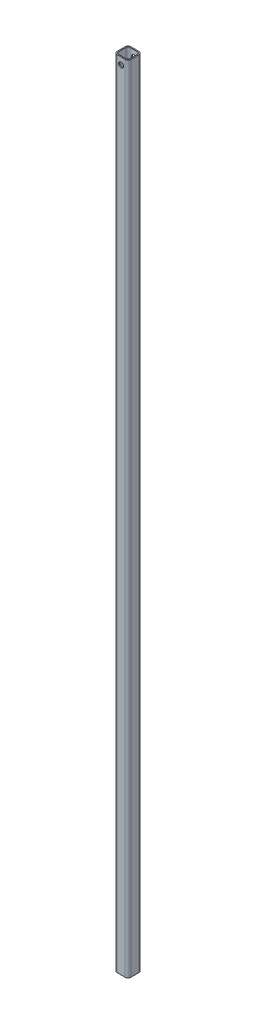
SolidWorks part; units mm, degrees
material "Plain Carbon Steel"
ref_plane "Front Plane" through (0, 0, 0) normal (0, 0, 1) x (1, 0, 0)
ref_plane "Top Plane" through (0, 0, 0) normal (0, 1, 0) x (1, 0, 0)
ref_plane "Right Plane" through (0, 0, 0) normal (1, 0, 0) x (0, 0, -1)
sketch "Sketch1" plane through (0, 0, 0) normal (0, 1, 0) x (1, 0, 0)
  line L0 (-8.6995, -13.462) -> (8.6995, -13.462)
  line L1 (-13.462, -8.6995) -> (-13.462, 8.6995)
  line L2 (8.6995, 13.462) -> (-8.6995, 13.462)
  line L3 (13.462, 8.6995) -> (13.462, -8.6995)
  line L4 (-9.525, -15.875) -> (9.525, -15.875)
  line L5 (-15.875, -9.525) -> (-15.875, 9.525)
  line L6 (9.525, 15.875) -> (-9.525, 15.875)
  line L7 (15.875, 9.525) -> (15.875, -9.525)
  line L8 (0, 13.462) -> (0, -13.462) construction
  arc A0 (15.875, 9.525) -> (9.525, 15.875) centre (9.525, 9.525) ccw
  arc A1 (9.525, -15.875) -> (15.875, -9.525) centre (9.525, -9.525) ccw
  arc A2 (-15.875, -9.525) -> (-9.525, -15.875) centre (-9.525, -9.525) ccw
  arc A3 (-9.525, 15.875) -> (-15.875, 9.525) centre (-9.525, 9.525) ccw
  arc A4 (-8.6995, 13.462) -> (-13.462, 8.6995) centre (-8.6995, 8.6995) ccw
  arc A5 (13.462, 8.6995) -> (8.6995, 13.462) centre (8.6995, 8.6995) ccw
  arc A6 (8.6995, -13.462) -> (13.462, -8.6995) centre (8.6995, -8.6995) ccw
  arc A7 (-13.462, -8.6995) -> (-8.6995, -13.462) centre (-8.6995, -8.6995) ccw
extrude "Boss-Extrude1" add sketch "Sketch1" along normal mid plane 1828.8
sketch "Sketch2" plane through (0, 0, 15.875) normal (0, 0, 1) x (1, 0, 0)
  line L0 (-9.525, 914.4) -> (9.525, 914.4) construction
  line L1 (0, -17.4625) -> (0, 17.4625) construction
  circle A0 centre (0, 898.525) radius 5.715
  dimension "D2" = 11.43
  dimension "D1" = 15.875
extrude "Cut-Extrude1" cut sketch "Sketch2" against normal through all
